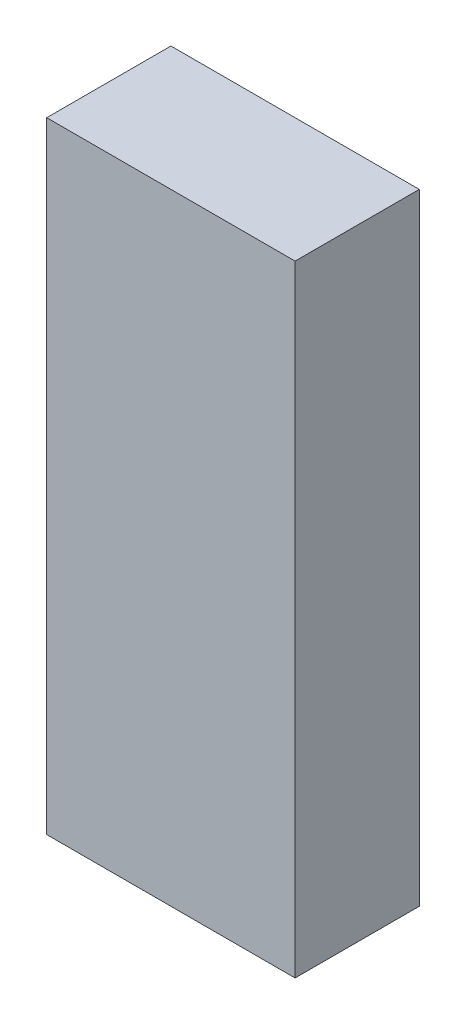
SolidWorks part; units mm, degrees
ref_plane "Front Plane" through (0, 0, 0) normal (0, 0, 1) x (1, 0, 0)
ref_plane "Top Plane" through (0, 0, 0) normal (0, 1, 0) x (1, 0, 0)
ref_plane "Right Plane" through (0, 0, 0) normal (1, 0, 0) x (0, 0, -1)
sketch "Sketch1" plane through (0, 0, 0) normal (0, 1, 0) x (1, 0, 0)
  line L1 (0, 0) -> (200, 0)
  line L2 (0, 0) -> (0, 100)
  line L3 (0, 100) -> (200, 100)
  line L4 (200, 0) -> (200, 100)
extrude "Boss-Extrude1" add sketch "Sketch1" along normal blind 500
